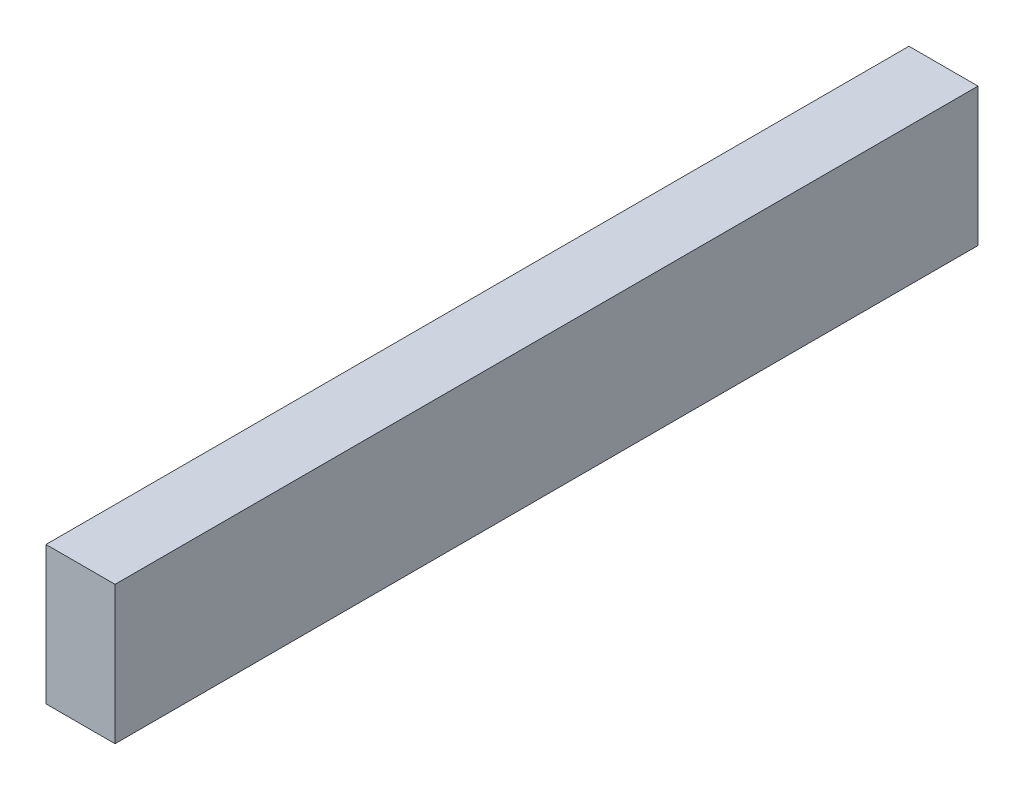
SolidWorks part; units mm, degrees
ref_plane "Front Plane" through (0, 0, 0) normal (0, 0, 1) x (1, 0, 0)
ref_plane "Top Plane" through (0, 0, 0) normal (0, 1, 0) x (1, 0, 0)
ref_plane "Right Plane" through (0, 0, 0) normal (1, 0, 0) x (0, 0, -1)
sketch "Sketch2" plane through (0, 0, 0) normal (1, 0, 0) x (0, 0, -1)
  line L3 (-262.7936, 0) -> (0, 0)
  line L4 (0, 0) -> (165.1, 0)
  line L6 (165.1, 0) -> (165.1, 81.9)
  line L7 (165.1, 81.9) -> (150.1, 81.9)
  line L8 (150.1, 81.9) -> (150.1, 20)
  line L9 (150.1, 20) -> (0, 20)
  line L10 (0, 20) -> (0, 133.7)
  line L11 (0, 133.7) -> (-115, 133.7)
  line L12 (-115, 133.7) -> (-171.1938, 94.3527)
  line L13 (-171.1938, 94.3527) -> (-262.7936, 81.4791)
  line L18 (-262.7936, 81.4791) -> (-262.7936, 31.4791)
  line L19 (-262.7936, 31.4791) -> (-262.7936, 0) construction
  arc A2 (-262.7936, 31.4791) -> (-262.7936, 0) centre (-255.1441, 15.7396) ccw
  dimension "D12" = 17.5
  dimension "D2" = 113.7
  dimension "D3" = 20
  dimension "D4" = 35
  dimension "D5" = 153
  dimension "D6" = 165.1
  dimension "D7" = 15
  dimension "D8" = 61.9
  dimension "D9" = 92.5
  dimension "D10" = 68.6
  dimension "D11" = 50
  dimension "D13" = 115
extrude "Boss-Extrude1" add sketch "Sketch2" along normal mid plane 138
sketch "Sketch4" plane through (0, 20, 0) normal (0, 1, 0) x (1, 0, 0)
  line L0 (69, 150.1) -> (-69, 150.1) construction
  line L1 (69, 0) -> (54, 0)
  line L2 (69, 0) -> (69, 150.1)
  line L3 (69, 150.1) -> (54, 150.1)
  line L4 (54, 0) -> (54, 150.1)
  dimension "D1" = 15
extrude "Boss-Extrude2" add sketch "Sketch4" along normal up to surface (61.9 mm away) up to face at (0, 81.9, -157.6)
mirror "Mirror1" about plane through (0, 0, 0) normal (1, 0, 0) of "Boss-Extrude2"
sketch "Sketch5" plane through (69, 0, 0) normal (1, 0, 0) x (0, 0, -1)
  line L0 (-262.7936, 0) -> (165.1, 0) construction
  line L1 (-224.9441, 0) -> (-160.3441, 0)
  line L2 (28.0559, 0) -> (92.6559, 0)
  arc A0 (-224.9441, 0) -> (-160.3441, 0) centre (-192.6441, 0) ccw
  arc A1 (28.0559, 0) -> (92.6559, 0) centre (60.3559, 0) ccw
  arc A2 (-262.7936, 31.4791) -> (-262.7936, 0) centre (-255.1441, 15.7396) ccw construction
  point P11 (-272.6441, 15.7396)
  dimension "D3" = 32.3
  dimension "D1" = 333
  dimension "D2" = 80
extrude "Boss-Extrude3" add sketch "Sketch5" against normal blind 20.4
mirror "Mirror2" about plane through (0, 0, 0) normal (1, 0, 0) of "Boss-Extrude3"
fillet "Fillet1" radius 10 5 edges at (0, 133.7, 0) (0, 133.7, 115) (0, 94.3527, 171.1938) (0, 81.4791, 262.7936) (0, 31.4791, 262.7936)
sketch "Sketch6" plane through (0, 0, 0) normal (1, 0, 0) x (0, 0, -1)
  line L0 (-192.6441, 0) -> (-192.6441, -32.3) construction
  line L1 (-692.6441, -32.3) -> (1207.3559, -32.3)
  line L2 (-692.6441, -32.3) -> (-692.6441, 271.7)
  line L3 (-692.6441, 271.7) -> (1207.3559, 271.7)
  line L4 (1207.3559, -32.3) -> (1207.3559, 271.7)
  arc A0 (-224.9441, 0) -> (-160.3441, 0) centre (-192.6441, 0) ccw construction
  dimension "D1" = 304
  dimension "D2" = 1900
  dimension "D3" = 500
extrude "Boss-Extrude4" add sketch "Sketch6" along normal blind 152 separate body
